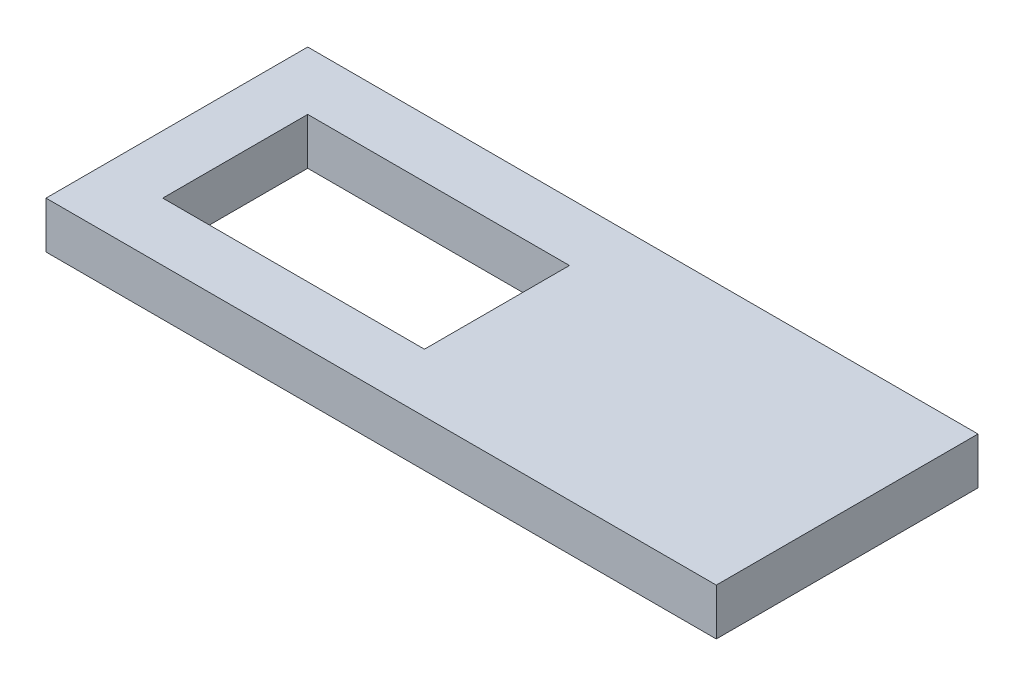
SolidWorks part; units mm, degrees
ref_plane "Front Plane" through (0, 0, 0) normal (0, 0, 1) x (1, 0, 0)
ref_plane "Top Plane" through (0, 0, 0) normal (0, 1, 0) x (1, 0, 0)
ref_plane "Right Plane" through (0, 0, 0) normal (1, 0, 0) x (0, 0, -1)
sketch "Sketch1" plane through (0, 0, 0) normal (0, 1, 0) x (1, 0, 0)
  line L1 (0, 0) -> (22.42, 0)
  line L2 (0, 0) -> (0, 12.42)
  line L3 (0, 12.42) -> (22.42, 12.42)
  line L4 (22.42, 0) -> (22.42, 12.42)
  line L5 (-5, 17.42) -> (52.42, 17.42)
  line L6 (-5, 17.42) -> (-5, -5)
  line L7 (-5, -5) -> (52.42, -5)
  line L8 (52.42, 17.42) -> (52.42, -5)
  point P9 (0, 6.21)
  point P10 (-5, 6.21)
  point P11 (22.42, 6.21)
  dimension "D1" = 5
  dimension "D2" = 22.42
  dimension "D3" = 12.42
  dimension "D4" = 30
  dimension "D5" = 5
extrude "Boss-Extrude1" add sketch "Sketch1" along normal blind 4
